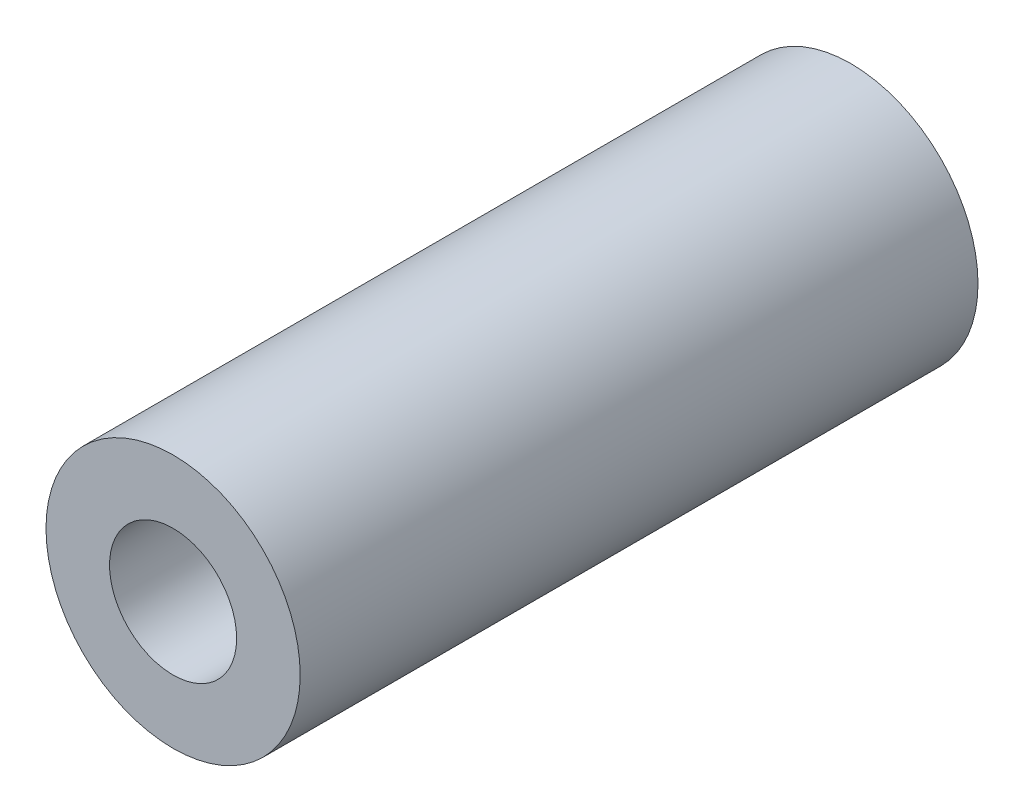
SolidWorks part; units mm, degrees
ref_plane "Front Plane" through (0, 0, 0) normal (0, 0, 1) x (1, 0, 0)
ref_plane "Top Plane" through (0, 0, 0) normal (0, 1, 0) x (1, 0, 0)
ref_plane "Right Plane" through (0, 0, 0) normal (1, 0, 0) x (0, 0, -1)
sketch "Esquisse1" plane through (0, 0, 0) normal (0, 0, 1) x (1, 0, 0)
  circle A0 centre (0, 0) radius 1.5
  circle A1 centre (0, 0) radius 3
  dimension "D1" = 6
  dimension "D2" = 3
extrude "Main" add sketch "Esquisse1" along normal blind 16
